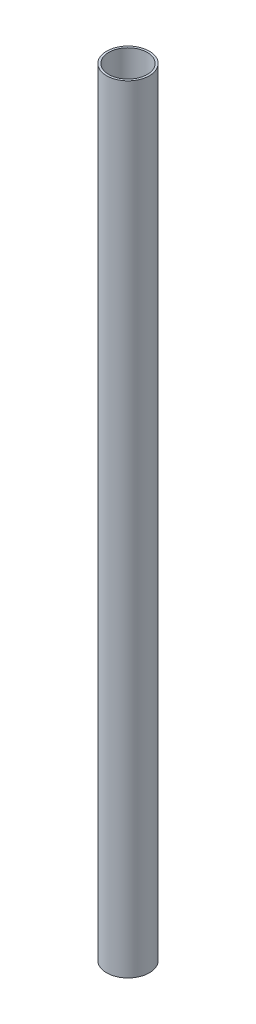
SolidWorks part; units mm, degrees
material "Glass"
ref_plane "Front Plane" through (0, 0, 0) normal (0, 0, 1) x (1, 0, 0)
ref_plane "Top Plane" through (0, 0, 0) normal (0, 1, 0) x (1, 0, 0)
ref_plane "Right Plane" through (0, 0, 0) normal (1, 0, 0) x (0, 0, -1)
sketch "Sketch1" plane through (0, 0, 0) normal (0, 1, 0) x (1, 0, 0)
  circle A0 centre (0, 0) radius 14.2875
  circle A1 centre (0, 0) radius 15.875
  dimension "D1" = 28.575
  dimension "D2" = 31.75
extrude "Boss-Extrude1" add sketch "Sketch1" along normal blind 577.85
